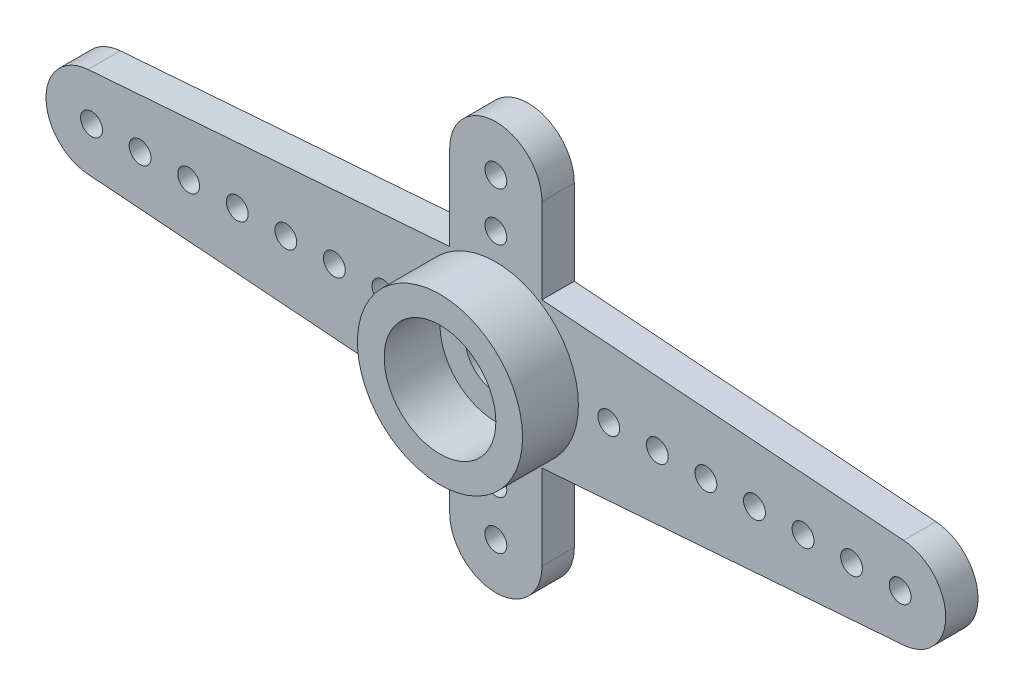
SolidWorks part; units mm, degrees
ref_plane "Ebene vorne" through (0, 0, 0) normal (0, 0, 1) x (1, 0, 0)
ref_plane "Ebene oben" through (0, 0, 0) normal (0, 1, 0) x (1, 0, 0)
ref_plane "Ebene rechts" through (0, 0, 0) normal (1, 0, 0) x (0, 0, -1)
sketch "Skizze1" plane through (0, 0, 0) normal (0, 0, 1) x (1, 0, 0)
  line L0 (0, 3) -> (0, 0) construction
  line L1 (16.65, 0) -> (-16.65, 0) construction
  line L2 (-16.7919, 1.8696) -> (-1.9, 3)
  line L4 (-16.7919, -1.8696) -> (-1.9, -3)
  line L5 (16.7919, -1.8696) -> (1.9, -3)
  line L6 (16.7919, 1.8696) -> (1.9, 3)
  line L7 (-1.9, 3) -> (-1.9, 6.5)
  line L8 (1.9, 3) -> (1.9, 6.5)
  line L9 (1.9, -3) -> (1.9, -6.5)
  line L10 (-1.9, -3) -> (-1.9, -6.5)
  arc A0 (-16.7919, 1.8696) -> (-16.7919, -1.8696) centre (-16.65, 0) ccw
  arc A1 (16.7919, 1.8696) -> (16.7919, -1.8696) centre (16.65, 0) cw
  arc A2 (1.9, 6.5) -> (-1.9, 6.5) centre (0, 6.5) ccw
  arc A3 (1.9, -6.5) -> (-1.9, -6.5) centre (0, -6.5) cw
  dimension "D1" = 3.75
  dimension "D5" = 13
  dimension "D6" = 1.9
  dimension "D2" = 33.3
  dimension "D3" = 6
  dimension "D4" = 3.8
extrude "Aufsatz-Linear austragen1" add sketch "Skizze1" along normal blind 1.33
sketch "Skizze2" plane through (0, 0, 1.33) normal (0, 0, 1) x (1, 0, 0)
  circle A0 centre (0, 0) radius 3.4
  circle A1 centre (0, 0) radius 2.3
  dimension "D1" = 6.8
  dimension "D2" = 4.6
extrude "Aufsatz-Linear austragen2" add sketch "Skizze2" along normal blind 2.3 and the other way up to surface (1.33 mm away) other way up to face at (0, 0, 0)
sketch "Skizze3" plane through (0, 0, 1.33) normal (0, 0, 1) x (1, 0, 0)
  circle A0 centre (0, 0) radius 1.25
  dimension "D1" = 2.5
extrude "Schnitt-Linear austragen1" cut sketch "Skizze3" against normal through all
sketch "Skizze4" plane through (0, 0, 0) normal (0, 0, -1) x (-1, 0, 0)
  circle A0 centre (0, 0) radius 2.35
  dimension "D1" = 4.7
extrude "Schnitt-Linear austragen2" cut sketch "Skizze4" against normal blind 1.1
sketch "Skizze5" plane through (0, 0, 1.33) normal (0, 0, 1) x (1, 0, 0)
  line L0 (0, 6.5) -> (0, 0) construction
  line L1 (0, 0) -> (-16.65, 0) construction
  line L2 (0, 4.5) -> (0, -2) construction
  circle A0 centre (0, 6.5) radius 0.45
  circle A1 centre (-16.65, 0) radius 0.45
  circle A2 centre (0, 4.5) radius 0.45
  circle A3 centre (-14.65, 0) radius 0.45
  circle A4 centre (-12.65, 0) radius 0.45
  circle A5 centre (-10.65, 0) radius 0.45
  circle A6 centre (-8.65, 0) radius 0.45
  circle A7 centre (-6.65, 0) radius 0.45
  circle A8 centre (-4.65, 0) radius 0.45
  circle A9 centre (0, -4.5) radius 0.45
  circle A10 centre (0, -6.5) radius 0.45
  circle A11 centre (4.65, 0) radius 0.45
  circle A12 centre (6.65, 0) radius 0.45
  circle A13 centre (8.65, 0) radius 0.45
  circle A14 centre (10.65, 0) radius 0.45
  circle A15 centre (12.65, 0) radius 0.45
  circle A16 centre (14.65, 0) radius 0.45
  circle A17 centre (16.65, 0) radius 0.45
  dimension "D1" = 0.9
  dimension "D2" = 2
  dimension "D3" = 7
extrude "Schnitt-Linear austragen3" cut sketch "Skizze5" against normal through all
